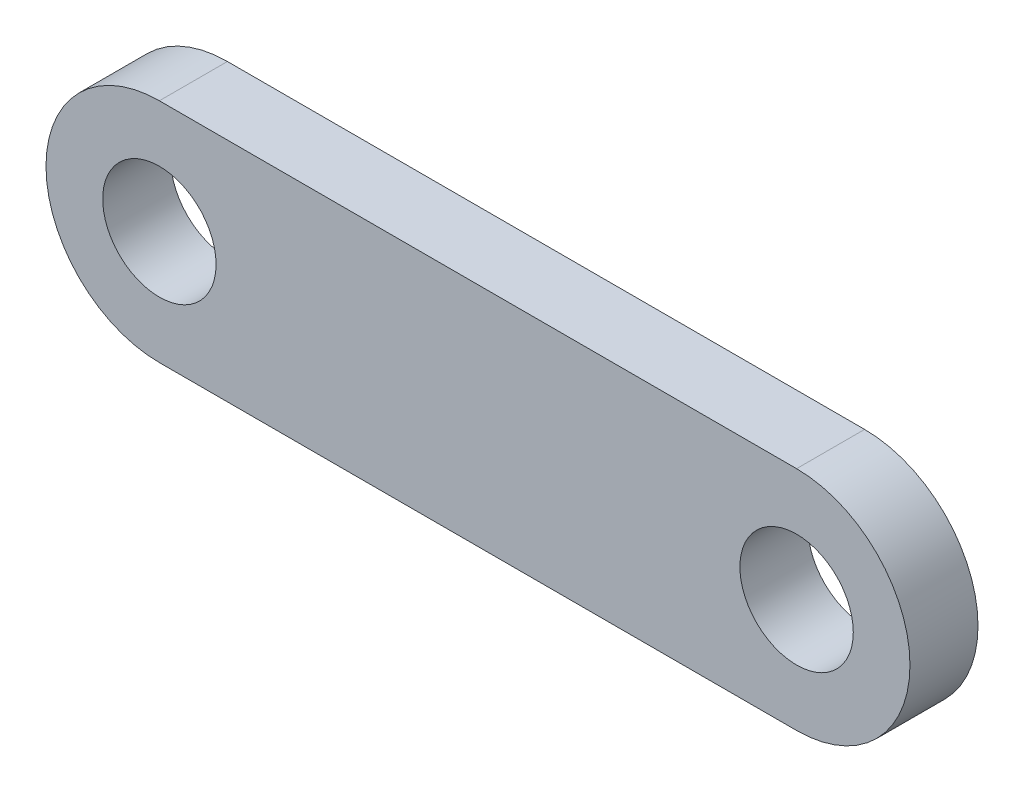
SolidWorks part; units mm, degrees
ref_plane "Alzado" through (0, 0, 0) normal (0, 0, 1) x (1, 0, 0)
ref_plane "Planta" through (0, 0, 0) normal (0, 1, 0) x (1, 0, 0)
ref_plane "Vista lateral" through (0, 0, 0) normal (1, 0, 0) x (0, 0, -1)
sketch "Croquis1" plane through (0, 0, 0) normal (0, 0, 1) x (1, 0, 0)
  line L0 (-28.7828, 0) -> (27.4172, 0) construction
  line L1 (-28.7828, 10) -> (27.4172, 10)
  line L2 (-28.7828, -10) -> (27.4172, -10)
  arc A0 (-28.7828, 10) -> (-28.7828, -10) centre (-28.7828, 0) ccw
  arc A1 (27.4172, -10) -> (27.4172, 10) centre (27.4172, 0) ccw
  circle A2 centre (-28.7828, 0) radius 5
  circle A3 centre (27.4172, 0) radius 5
  point P3 (-0.6828, 0)
  dimension "D1" = 10
  dimension "D3" = 10
  dimension "D2" = 56.2
extrude "Saliente-Extruir1" add sketch "Croquis1" along normal blind 6
